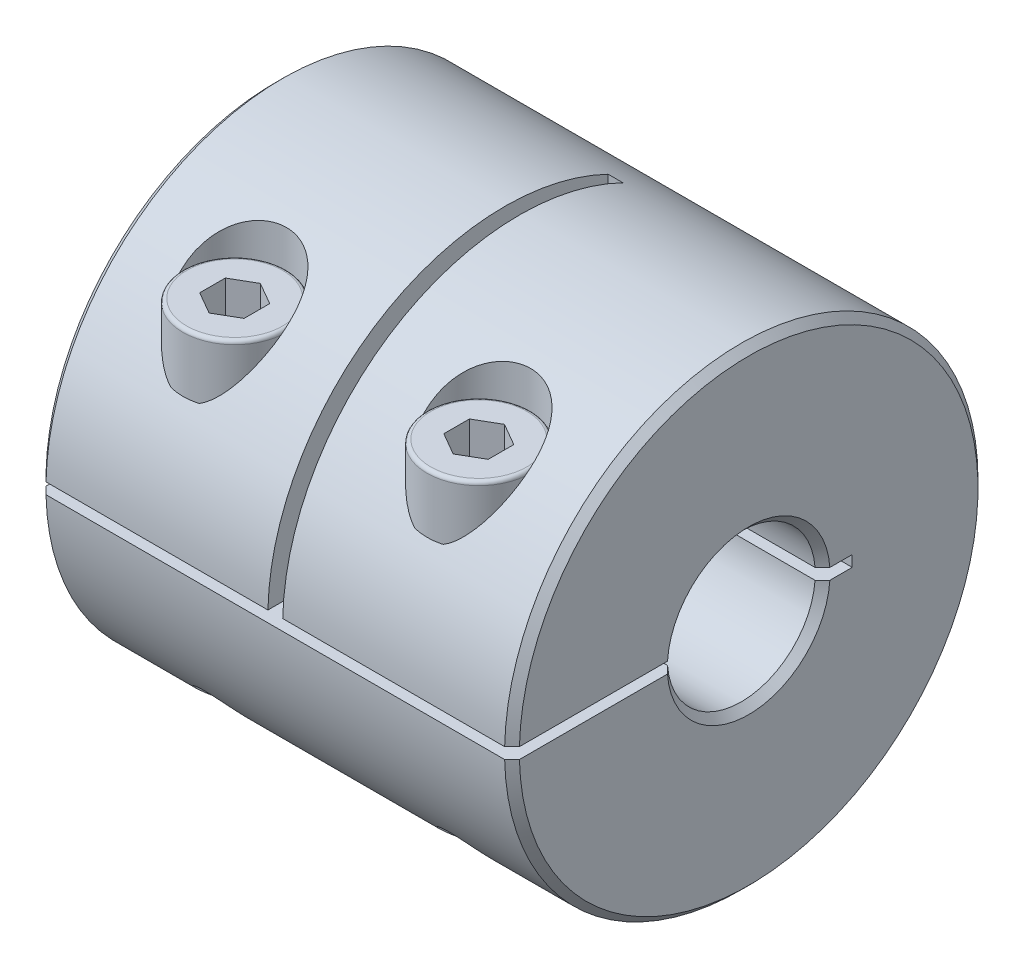
SolidWorks part; units mm, degrees
ref_plane "Front Plane" through (0, 0, 0) normal (0, 0, 1) x (1, 0, 0)
ref_plane "Top Plane" through (0, 0, 0) normal (0, 1, 0) x (1, 0, 0)
ref_plane "Right Plane" through (0, 0, 0) normal (1, 0, 0) x (0, 0, -1)
sketch "Sketch1" plane through (0, 0, 0) normal (1, 0, 0) x (0, 0, -1)
  circle A0 centre (0, 0) radius 16
  dimension "Dim D" = 32
extrude "Boss-Extrude1" add sketch "Sketch1" along normal mid plane 32
sketch "Sketch2" plane through (16, 0, 0) normal (1, 0, 0) x (0, 0, -1)
  circle A0 centre (0, 0) radius 5
  dimension "Dim d2" = 10
extrude "Cut-Extrude1" cut sketch "Sketch2" against normal through all
sketch "Sketch5" plane through (16, 0, 0) normal (1, 0, 0) x (0, 0, -1)
  line L0 (0, 0) -> (7, 0) construction
  line L1 (-15.9956, 0.375) -> (7, 0.375)
  line L2 (5, 0.375) -> (5, -0.375) construction
  line L3 (-15.9956, -0.375) -> (7, -0.375)
  line L4 (7, 0.375) -> (7, -0.375)
  circle A0 centre (0, 0) radius 16 construction
  arc A1 (-15.9956, 0.375) -> (-15.9956, -0.375) centre (0, 0) ccw
  circle A2 centre (0, 0) radius 5 construction
  dimension "D1" = 0.75
  dimension "D2" = 2
extrude "Cut-Extrude2" cut sketch "Sketch5" against normal through all
sketch "Sketch6" plane through (0, 0, -7) normal (0, 0, 1) x (1, 0, 0)
  line L0 (-16, -0.375) -> (16, -0.375) construction
  line L1 (-0.5, -0.375) -> (0.5, -0.375)
  line L2 (-0.5, -0.375) -> (-0.5, 16)
  line L3 (-0.5, 16) -> (0.5, 16)
  line L4 (0.5, -0.375) -> (0.5, 16)
  line L5 (16, 16) -> (-16, 16) construction
  line L6 (0, 0) -> (0, 16) construction
  line L7 (16, -16) -> (16, 16) construction
  dimension "Dim L2" = 15.5
extrude "Cut-Extrude3" cut sketch "Sketch6" along normal through all
sketch "Sketch7" plane through (0, -0.375, 0) normal (0, 1, 0) x (1, 0, 0)
  line L0 (8.25, -4.9859) -> (8.25, -15.9956) construction
  line L1 (16, -4.9859) -> (0.5, -4.9859) construction
  line L2 (0.5, -15.9956) -> (16, -15.9956) construction
  line L3 (16, -15.9956) -> (16, 16) construction
  circle A0 centre (8.25, -10.4908) radius 2
  dimension "Dim M" = 4
  dimension "Dim L1" = 7.75
extrude "Cut-Extrude4" cut sketch "Sketch7" against normal through all and the other way through all
ref_plane "Plane1" through (0, 16, 0) normal (0, 1, 0) x (-1, 0, 0)
ref_plane "Plane2" through (0, 8, 0) normal (0, 1, 0) x (-1, 0, 0)
sketch "Sketch8" plane through (0, 8, 0) normal (0, 1, 0) x (-1, 0, 0)
  circle A0 centre (-8.25, 10.4908) radius 3.5
  dimension "Dim bolt diameter" = 7
extrude "Cut-Extrude5" cut sketch "Sketch8" along normal through all
mirror "Mirror1" about plane through (0, 0, 0) normal (1, 0, 0) of "Cut-Extrude5", "Cut-Extrude4"
ref_plane "Plane4" through (0, -16, 0) normal (0, -1, 0) x (1, 0, 0)
ref_plane "Plane5" through (0, -8, 0) normal (0, -1, 0) x (1, 0, 0)
sketch "Sketch9" plane through (0, 8, 0) normal (0, 1, 0) x (1, 0, 0)
  circle A0 centre (8.25, -10.4908) radius 3.5
  circle A1 centre (8.25, -10.4908) radius 3.5 construction
extrude "Boss-Extrude2" add sketch "Sketch9" along normal blind 4 separate body
sketch "Sketch10" plane through (0, 12, 0) normal (0, 1, 0) x (1, 0, 0)
  circle A0 centre (8.25, -10.4908) radius 2 construction
  circle A1 centre (8.25, -10.4908) radius 2
extrude "Boss-Extrude3" add sketch "Sketch10" against normal up to surface (20 mm away) up to plane "Plane5"
fillet "Fillet1" radius 0.25 2 edges at (8.25, -8, 8.4908) (8.25, 12, 13.9908)
sketch "Sketch11" plane through (0, 12, 0) normal (0, 1, 0) x (1, 0, 0)
  line L1 (8.25, -8.7587) -> (6.75, -9.6247)
  line L2 (6.75, -9.6247) -> (6.75, -11.3568)
  line L3 (6.75, -11.3568) -> (8.25, -12.2228)
  line L4 (8.25, -12.2228) -> (9.75, -11.3568)
  line L5 (9.75, -11.3568) -> (9.75, -9.6247)
  line L6 (9.75, -9.6247) -> (8.25, -8.7587)
  circle A0 centre (8.25, -10.4908) radius 1.5 construction
  dimension "Dim hex width" = 3
extrude "Cut-Extrude6" cut sketch "Sketch11" against normal blind 3
mirror "Mirror2" about plane through (0, 0, 0) normal (1, 0, 0) of bodies 111
chamfer "Chamfer1" distance 0.5 angle 45 6 edges at (-16, 0, -16) (16, 0, -16) (-16, 5, 0) (-16, -5, 0) (16, -5, 0) (16, 5, 0)
